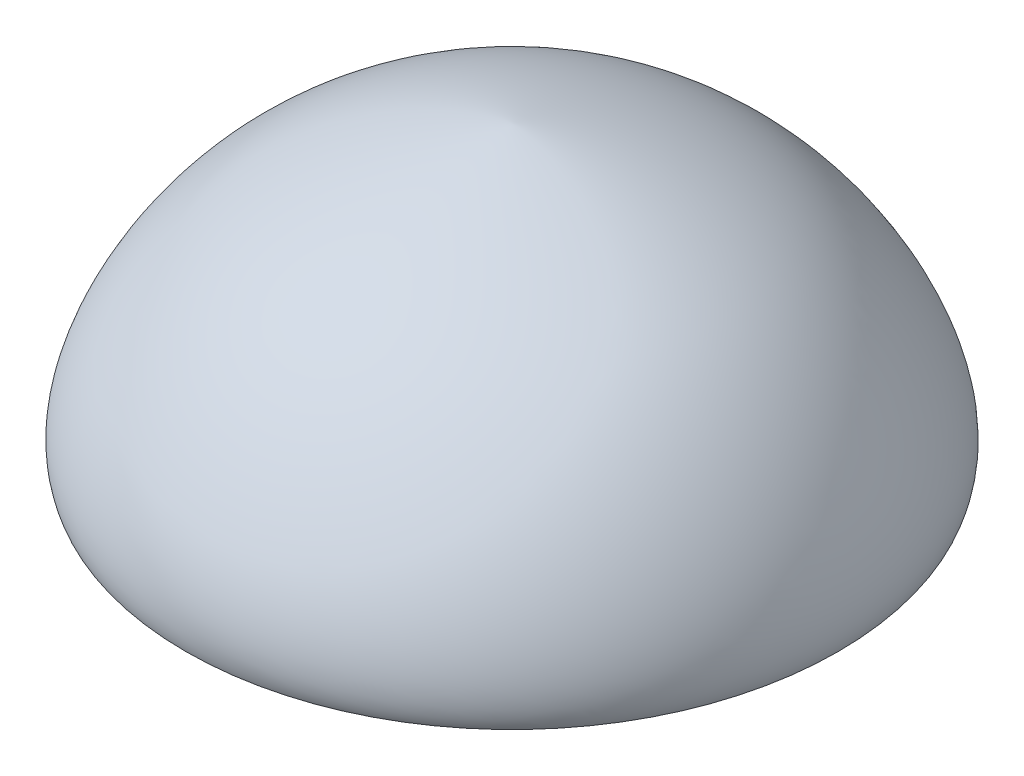
SolidWorks part; units mm, degrees
ref_plane "Front Plane" through (0, 0, 0) normal (0, 0, 1) x (1, 0, 0)
ref_plane "Top Plane" through (0, 0, 0) normal (0, 1, 0) x (1, 0, 0)
ref_plane "Right Plane" through (0, 0, 0) normal (1, 0, 0) x (0, 0, -1)
sketch "Sketch1" plane through (0, 0, 0) normal (0, 0, 1) x (1, 0, 0)
  line L0 (0, 0.45) -> (0, 0)
  line L1 (0, 0) -> (0.5, 0)
  line L2 (0, 0.45) -> (-0.2263, 0.45) construction
  line L3 (0.5, 0) -> (0.4442, -0.1368) construction
  spline S0 degree 3 poles (0.5, 0) (0.5254, 0.0623) (0.3897, 0.3789) (0.0255, 0.45) (0, 0.45) knots 0 0 0 0 0.503823 1 1 1 1
  point P5 (0.2266, 0.1717)
  point P8 (0.3307, 0.319)
  dimension "D1" = 0.45
  dimension "D2" = 0.5
revolve "Revolve1" add sketch "Sketch1" angle 360 about L0
